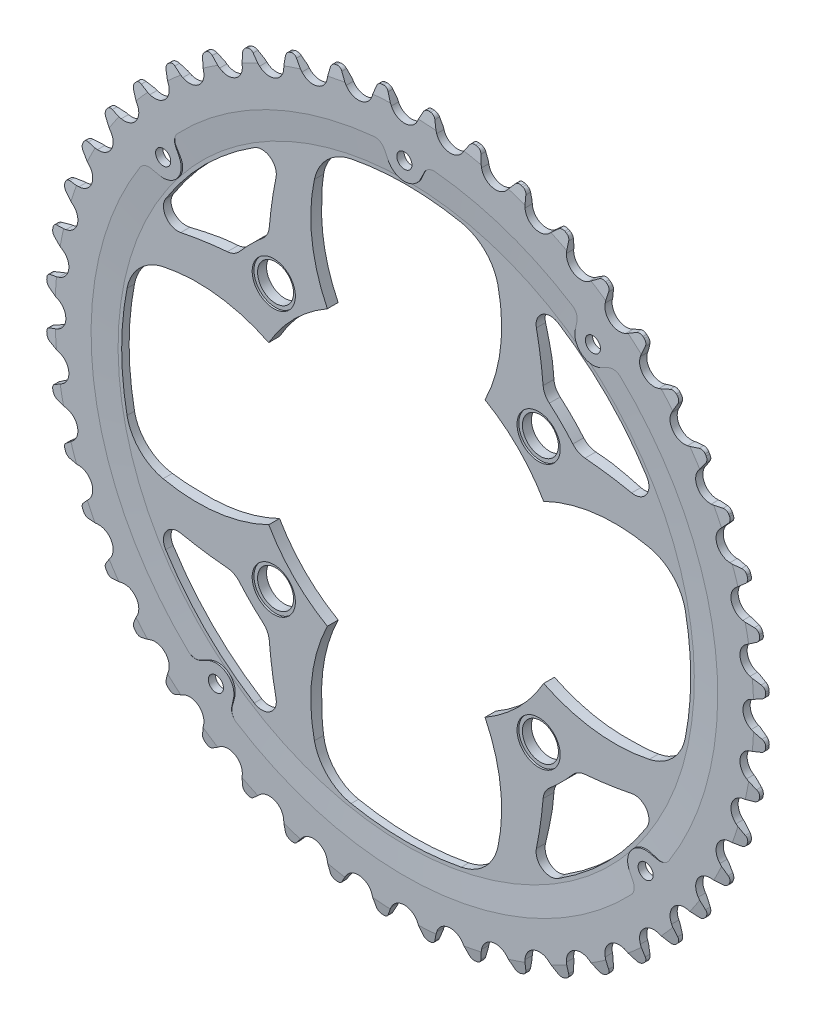
SolidWorks part; units mm, degrees
ref_plane "Plan de face" through (0, 0, 0) normal (0, 0, 1) x (1, 0, 0)
ref_plane "Plan de dessus" through (0, 0, 0) normal (0, 1, 0) x (1, 0, 0)
ref_plane "Plan de droite" through (0, 0, 0) normal (1, 0, 0) x (0, 0, -1)
sketch "Esquisse7" plane through (0, 0, 0) normal (1, 0, 0) x (0, 0, -1)
  line L0 (-21.1331, 0) -> (18.4676, 0) construction
  line L1 (0, 44) -> (2.5, 44)
  line L2 (-1, 100) -> (1, 100)
  line L3 (0, 0) -> (0, 124.4372) construction
  line L4 (2.5, 44) -> (2.5, 66)
  line L5 (-0.5, 80) -> (-1, 87)
  line L6 (-0.5, 44) -> (-0.5, 80)
  line L7 (1, 87) -> (2.5, 66)
  line L8 (-1, 87) -> (-1, 100)
  line L9 (1, 87) -> (1, 100)
  line L10 (2.5, 66) -> (2.5656, 65.8539) construction
  line L11 (-0.5, 80) -> (5.3022, 67.0831) construction
  line L12 (-0.5, 44) -> (0, 44)
  dimension "D1" = 88
  dimension "D2" = 200
  dimension "D4" = 2
  dimension "D5" = 2.5
  dimension "D6" = 160
  dimension "D7" = 174
  dimension "D3" = 3
revolve "Révolution1" add sketch "Esquisse7" angle 360 about L0
ref_plane "Plan1" through (0, 0, 0) normal (-0.788, 0.6157, 0) x (0, 0, 1)
sketch "Esquisse4" plane through (0, 0, 0) normal (1, 0, 0) x (0, 0, -1)
  line L0 (-6.7593, 0) -> (13.1966, 0) construction
  line L1 (-1, 100) -> (-0.5, 100)
  line L2 (-0.5, 100) -> (-1, 97)
  line L4 (-1, 97) -> (-1, 100)
  line L5 (0, 0) -> (0, 63.6893) construction
  line L6 (1, 100) -> (0.5, 100)
  line L7 (0.5, 100) -> (1, 97)
  line L8 (1, 97) -> (1, 100)
  line L9 (1, 100) -> (-1, 100) construction
  line L10 (-1, 100) -> (-1, -100) construction
  dimension "D1" = 3
  dimension "D2" = 1
revolve "Enlèvement de matière-Révolution1" cut sketch "Esquisse4" angle 360 about L0
sketch "Esquisse2" plane through (0, 0, 0) normal (0, 0, 1) x (1, 0, 0)
  line L0 (0, 0) -> (0, 69.4312) construction
  line L1 (-4.8509, 98.938) -> (-3.6252, 96.3095)
  line L2 (4.8509, 98.938) -> (3.6252, 96.3095)
  line L3 (0, 0) -> (87.6932, 0) construction
  arc A0 (-3.6252, 96.3095) -> (3.6252, 96.3095) centre (0, 98) ccw
  arc A1 (-4.8509, 98.938) -> (-6.3049, 99.801) centre (-6.2103, 98.304) ccw
  arc A2 (6.3049, 99.801) -> (-6.3049, 99.801) centre (0, 0) ccw
  arc A4 (4.8509, 98.938) -> (6.3049, 99.801) centre (6.2103, 98.304) cw
  circle A5 centre (0, 0) radius 100 construction
  dimension "D1" = 8
  dimension "D3" = 2
  dimension "D4" = 1.5
  dimension "D2" = 25
extrude "Enlèv. mat.-Extru.1" cut sketch "Esquisse2" against normal through all and the other way through all
pattern_circular "Répétition circulaire1" count 48 every 7.5 about axis through (0, 0, 0) along (0, 0, 1) of "Enlèv. mat.-Extru.1"
sketch "Esquisse5" plane through (0, 0, 0) normal (0, 0, 1) x (1, 0, 0)
  line L0 (0, 0) -> (40.1862, 0) construction
  line L1 (0, 0) -> (0, 40.1862) construction
  line L2 (0, 0) -> (-60.8251, 60.8251) construction
  line L3 (0, 0) -> (60.8251, 60.8251) construction
  circle A0 centre (0, 0) radius 52 construction
  circle A1 centre (-36.7696, 36.7696) radius 5
  circle A2 centre (36.7696, 36.7696) radius 5
  circle A3 centre (-36.7696, -36.7696) radius 5
  circle A4 centre (36.7696, -36.7696) radius 5
  dimension "D1" = 104
  dimension "D2" = 10
  dimension "D3" = 90
extrude "Enlèv. mat.-Extru.2" cut sketch "Esquisse5" against normal through all and the other way through all
sketch "Esquisse11" plane through (0, 0, 0.5) normal (0, 0, 1) x (1, 0, 0)
  circle A0 centre (36.7696, 36.7696) radius 6
  circle A1 centre (-36.7696, 36.7696) radius 6
  circle A2 centre (-36.7696, -36.7696) radius 6
  circle A3 centre (36.7696, -36.7696) radius 6
  circle A4 centre (36.7696, 36.7696) radius 5 construction
  circle A5 centre (-36.7696, 36.7696) radius 5 construction
  circle A6 centre (-36.7696, -36.7696) radius 5 construction
  circle A7 centre (36.7696, -36.7696) radius 5 construction
  dimension "D1" = 12
extrude "Enlèv. mat.-Extru.7" cut sketch "Esquisse11" against normal blind 0.5
sketch "Esquisse8" plane through (0, 0, 1) normal (0, 0, 1) x (1, 0, 0)
  line L0 (47.9272, 70.3104) -> (47.4405, 68.0205)
  line L1 (0, 0) -> (69.663, 89.1645) construction
  line L2 (56.6272, 63.5132) -> (54.5231, 62.4869)
  line L3 (0, 0) -> (110.6244, 0) construction
  line L4 (0, 0) -> (-3.7173, 30.2748) construction
  line L5 (0, 0) -> (-89.1645, 69.663) construction
  line L6 (-70.3104, 47.9272) -> (-68.0205, 47.4405)
  line L7 (-63.5132, 56.6272) -> (-62.4869, 54.5231)
  line L8 (-47.9272, -70.3104) -> (-47.4405, -68.0205)
  line L9 (-56.6272, -63.5132) -> (-54.5231, -62.4869)
  line L10 (70.3104, -47.9272) -> (68.0205, -47.4405)
  line L11 (63.5132, -56.6272) -> (62.4869, -54.5231)
  line L12 (0, 0) -> (8.1726, 23.7349) construction
  line L13 (-5.5202, 84.9123) -> (-4.494, 82.8081)
  line L14 (5.5202, 84.9123) -> (4.494, 82.8081)
  line L15 (0, 0) -> (0, 113.1514) construction
  arc A0 (47.4405, 68.0205) -> (54.5231, 62.4869) centre (52.3312, 66.9809) ccw
  circle A1 centre (0, 0) radius 87 construction
  circle A2 centre (0, 0) radius 85 construction
  arc A3 (60.0117, 62.9888) -> (56.6272, 63.5132) centre (57.9423, 60.8168) ccw
  arc A4 (46.5997, 73.4675) -> (47.9272, 70.3104) centre (44.9928, 70.9341) cw
  arc A5 (-73.4675, 46.5997) -> (-70.3104, 47.9272) centre (-70.9341, 44.9928) cw
  arc A6 (-62.4869, 54.5231) -> (-68.0205, 47.4405) centre (-66.9809, 52.3312) cw
  arc A7 (60.0117, 62.9888) -> (46.5997, 73.4675) centre (0, 0) ccw
  arc A8 (-62.9888, 60.0117) -> (-63.5132, 56.6272) centre (-60.8168, 57.9423) ccw
  arc A9 (-73.4675, 46.5997) -> (-62.9888, 60.0117) centre (0, 0) cw
  arc A10 (-46.5997, -73.4675) -> (-60.0117, -62.9888) centre (0, 0) cw
  arc A11 (-60.0117, -62.9888) -> (-56.6272, -63.5132) centre (-57.9423, -60.8168) ccw
  arc A12 (-46.5997, -73.4675) -> (-47.9272, -70.3104) centre (-44.9928, -70.9341) cw
  arc A13 (-54.5231, -62.4869) -> (-47.4405, -68.0205) centre (-52.3312, -66.9809) cw
  arc A14 (62.9888, -60.0117) -> (73.4675, -46.5997) centre (0, 0) ccw
  arc A15 (73.4675, -46.5997) -> (70.3104, -47.9272) centre (70.9341, -44.9928) cw
  arc A16 (68.0205, -47.4405) -> (62.4869, -54.5231) centre (66.9809, -52.3312) ccw
  arc A17 (62.9888, -60.0117) -> (63.5132, -56.6272) centre (60.8168, -57.9423) ccw
  arc A18 (-8.5101, 86.5828) -> (8.5101, 86.5828) centre (0, 0) cw
  arc A19 (8.5101, 86.5828) -> (5.5202, 84.9123) centre (8.2166, 83.5972) ccw
  arc A20 (-8.5101, 86.5828) -> (-5.5202, 84.9123) centre (-8.2166, 83.5972) cw
  arc A21 (4.494, 82.8081) -> (-4.494, 82.8081) centre (0, 85) cw
  dimension "D1" = 10
  dimension "D3" = 3
  dimension "D5" = 170
  dimension "D2" = 38
  dimension "D4" = 52
  dimension "D6" = 90
extrude "Extrusion1" add sketch "Esquisse8" against normal up to surface up to face at (80, 0, 0.5)
sketch "Esquisse9" plane through (0, 0, -1) normal (0, 0, -1) x (-1, 0, 0)
  line L0 (-47.4405, 68.0205) -> (-47.9272, 70.3104) construction
  line L1 (-56.6272, 63.5132) -> (-54.5231, 62.4869) construction
  line L2 (-47.4405, 68.0205) -> (-47.9272, 70.3104)
  line L3 (-56.6272, 63.5132) -> (-54.5231, 62.4869)
  line L4 (70.3104, 47.9272) -> (68.0205, 47.4405) construction
  line L5 (62.4869, 54.5231) -> (63.5132, 56.6272) construction
  line L6 (70.3104, 47.9272) -> (68.0205, 47.4405)
  line L7 (62.4869, 54.5231) -> (63.5132, 56.6272)
  line L8 (54.5231, -62.4869) -> (56.6272, -63.5132) construction
  line L9 (47.9272, -70.3104) -> (47.4405, -68.0205) construction
  line L10 (54.5231, -62.4869) -> (56.6272, -63.5132)
  line L11 (47.9272, -70.3104) -> (47.4405, -68.0205)
  line L12 (-70.3104, -47.9272) -> (-68.0205, -47.4405) construction
  line L13 (-62.4869, -54.5231) -> (-63.5132, -56.6272) construction
  line L14 (-70.3104, -47.9272) -> (-68.0205, -47.4405)
  line L15 (-62.4869, -54.5231) -> (-63.5132, -56.6272)
  line L16 (-4.494, 82.8081) -> (-5.5202, 84.9123) construction
  line L17 (5.5202, 84.9123) -> (4.494, 82.8081) construction
  line L18 (-4.494, 82.8081) -> (-5.5202, 84.9123)
  line L19 (5.5202, 84.9123) -> (4.494, 82.8081)
  arc A0 (-46.5997, 73.4675) -> (-47.9272, 70.3104) centre (-44.9928, 70.9341) ccw construction
  arc A1 (-49.2529, 63.0409) -> (-47.4405, 68.0205) centre (-52.3312, 66.9809) ccw construction
  arc A2 (-54.5231, 62.4869) -> (-49.2529, 63.0409) centre (-52.3312, 66.9809) ccw construction
  arc A3 (-56.6272, 63.5132) -> (-60.0117, 62.9888) centre (-57.9423, 60.8168) ccw construction
  arc A4 (-46.5997, 73.4675) -> (-47.9272, 70.3104) centre (-44.9928, 70.9341) ccw
  arc A5 (-49.2529, 63.0409) -> (-47.4405, 68.0205) centre (-52.3312, 66.9809) ccw
  arc A6 (-54.5231, 62.4869) -> (-49.2529, 63.0409) centre (-52.3312, 66.9809) ccw
  arc A7 (-56.6272, 63.5132) -> (-60.0117, 62.9888) centre (-57.9423, 60.8168) ccw
  arc A8 (-46.5997, 73.4675) -> (-60.0117, 62.9888) centre (0, 0) ccw
  arc A9 (-8.5101, 86.5828) -> (-46.5997, 73.4675) centre (0, 0) ccw construction
  arc A10 (73.4675, 46.5997) -> (70.3104, 47.9272) centre (70.9341, 44.9928) ccw construction
  arc A11 (62.4869, 54.5231) -> (68.0205, 47.4405) centre (66.9809, 52.3312) ccw construction
  arc A12 (63.5132, 56.6272) -> (62.9888, 60.0117) centre (60.8168, 57.9423) ccw construction
  arc A13 (73.4675, 46.5997) -> (70.3104, 47.9272) centre (70.9341, 44.9928) ccw
  arc A14 (62.4869, 54.5231) -> (68.0205, 47.4405) centre (66.9809, 52.3312) ccw
  arc A15 (63.5132, 56.6272) -> (62.9888, 60.0117) centre (60.8168, 57.9423) ccw
  arc A16 (62.9888, 60.0117) -> (73.4675, 46.5997) centre (0, 0) cw
  arc A17 (-8.5101, 86.5828) -> (-46.5997, 73.4675) centre (0, 0) ccw construction
  arc A18 (54.5231, -62.4869) -> (47.4405, -68.0205) centre (52.3312, -66.9809) ccw construction
  arc A19 (56.6272, -63.5132) -> (60.0117, -62.9888) centre (57.9423, -60.8168) ccw construction
  arc A20 (46.5997, -73.4675) -> (47.9272, -70.3104) centre (44.9928, -70.9341) ccw construction
  arc A21 (54.5231, -62.4869) -> (47.4405, -68.0205) centre (52.3312, -66.9809) ccw
  arc A22 (56.6272, -63.5132) -> (60.0117, -62.9888) centre (57.9423, -60.8168) ccw
  arc A23 (46.5997, -73.4675) -> (47.9272, -70.3104) centre (44.9928, -70.9341) ccw
  arc A24 (60.0117, -62.9888) -> (46.5997, -73.4675) centre (0, 0) cw
  arc A25 (-62.9888, -60.0117) -> (46.5997, -73.4675) centre (0, 0) ccw construction
  arc A26 (-73.4675, -46.5997) -> (-70.3104, -47.9272) centre (-70.9341, -44.9928) ccw construction
  arc A27 (-62.4869, -54.5231) -> (-68.0205, -47.4405) centre (-66.9809, -52.3312) ccw construction
  arc A28 (-63.5132, -56.6272) -> (-62.9888, -60.0117) centre (-60.8168, -57.9423) ccw construction
  arc A29 (-73.4675, -46.5997) -> (-70.3104, -47.9272) centre (-70.9341, -44.9928) ccw
  arc A30 (-62.4869, -54.5231) -> (-68.0205, -47.4405) centre (-66.9809, -52.3312) ccw
  arc A31 (-63.5132, -56.6272) -> (-62.9888, -60.0117) centre (-60.8168, -57.9423) ccw
  arc A32 (-62.9888, -60.0117) -> (-73.4675, -46.5997) centre (0, 0) cw
  arc A33 (-60.0117, 62.9888) -> (-73.4675, -46.5997) centre (0, 0) ccw construction
  arc A34 (-5.5202, 84.9123) -> (-8.5101, 86.5828) centre (-8.2166, 83.5972) ccw construction
  arc A35 (-4.494, 82.8081) -> (4.494, 82.8081) centre (0, 85) ccw construction
  arc A36 (8.5101, 86.5828) -> (5.5202, 84.9123) centre (8.2166, 83.5972) ccw construction
  arc A37 (-5.5202, 84.9123) -> (-8.5101, 86.5828) centre (-8.2166, 83.5972) ccw
  arc A38 (-4.494, 82.8081) -> (4.494, 82.8081) centre (0, 85) ccw
  arc A39 (8.5101, 86.5828) -> (5.5202, 84.9123) centre (8.2166, 83.5972) ccw
  arc A40 (-8.5101, 86.5828) -> (8.5101, 86.5828) centre (0, 0) cw
  arc A41 (-8.5101, 86.5828) -> (-46.5997, 73.4675) centre (0, 0) ccw construction
extrude "Enlèv. mat.-Extru.5" cut sketch "Esquisse9" along normal through all
sketch "Esquisse6" plane through (0, 0, 0) normal (0, 0, 1) x (1, 0, 0)
  circle A1 centre (52.3312, 66.9809) radius 2.1
  circle A2 centre (-66.9809, 52.3312) radius 2.1
  circle A3 centre (-52.3312, -66.9809) radius 2.1
  circle A4 centre (66.9809, -52.3312) radius 2.1
  arc A5 (47.4405, 68.0205) -> (54.5231, 62.4869) centre (52.3312, 66.9809) ccw construction
  arc A6 (68.0205, -47.4405) -> (62.4869, -54.5231) centre (66.9809, -52.3312) ccw construction
  arc A7 (-47.4405, -68.0205) -> (-54.5231, -62.4869) centre (-52.3312, -66.9809) ccw construction
  arc A8 (-68.0205, 47.4405) -> (-62.4869, 54.5231) centre (-66.9809, 52.3312) ccw construction
  circle A9 centre (0, 85) radius 2.1
  arc A11 (-4.494, 82.8081) -> (4.494, 82.8081) centre (0, 85) ccw construction
  dimension "D2" = 4.2
extrude "Enlèv. mat.-Extru.4" cut sketch "Esquisse6" against normal through all and the other way through all
sketch "Esquisse10" plane through (0, 0, 0.5) normal (0, 0, 1) x (1, 0, 0)
  line L0 (0, 0) -> (115.5873, 0) construction
  line L1 (0, 0) -> (0, 64.2408) construction
  line L2 (0, 0) -> (50.0683, 50.0683) construction
  arc A0 (77.5048, -15.297) -> (77.5048, 15.297) centre (0, 0) ccw
  arc A1 (38.1664, 21.8934) -> (67.4934, 25.4872) centre (58, -18.5) cw
  arc A3 (38.1664, -21.8934) -> (67.4934, -25.4872) centre (58, 18.5) ccw
  arc A4 (38.1664, -21.8934) -> (38.1664, 21.8934) centre (0, 0) ccw
  circle A5 centre (0, 0) radius 44 construction
  arc A6 (77.5048, 15.297) -> (67.4934, 25.4872) centre (64.7509, 12.7798) ccw
  arc A7 (67.4934, -25.4872) -> (77.5048, -15.297) centre (64.7509, -12.7798) ccw
  arc A8 (-67.4934, -25.4872) -> (-77.5048, -15.297) centre (-64.7509, -12.7798) cw
  arc A9 (-77.5048, 15.297) -> (-67.4934, 25.4872) centre (-64.7509, 12.7798) cw
  arc A10 (-38.1664, -21.8934) -> (-38.1664, 21.8934) centre (0, 0) cw
  arc A11 (-38.1664, -21.8934) -> (-67.4934, -25.4872) centre (-58, 18.5) cw
  arc A12 (-38.1664, 21.8934) -> (-67.4934, 25.4872) centre (-58, -18.5) ccw
  arc A13 (-77.5048, -15.297) -> (-77.5048, 15.297) centre (0, 0) cw
  arc A14 (-15.297, -77.5048) -> (15.297, -77.5048) centre (0, 0) ccw
  arc A15 (21.8934, -38.1664) -> (25.4872, -67.4934) centre (-18.5, -58) cw
  arc A16 (-21.8934, -38.1664) -> (-25.4872, -67.4934) centre (18.5, -58) ccw
  arc A17 (-21.8934, -38.1664) -> (21.8934, -38.1664) centre (0, 0) ccw
  arc A18 (15.297, -77.5048) -> (25.4872, -67.4934) centre (12.7798, -64.7509) ccw
  arc A19 (-25.4872, -67.4934) -> (-15.297, -77.5048) centre (-12.7798, -64.7509) ccw
  arc A20 (-25.4872, 67.4934) -> (-15.297, 77.5048) centre (-12.7798, 64.7509) cw
  arc A21 (15.297, 77.5048) -> (25.4872, 67.4934) centre (12.7798, 64.7509) cw
  arc A22 (-21.8934, 38.1664) -> (21.8934, 38.1664) centre (0, 0) cw
  arc A23 (-21.8934, 38.1664) -> (-25.4872, 67.4934) centre (18.5, 58) cw
  arc A24 (21.8934, 38.1664) -> (25.4872, 67.4934) centre (-18.5, 58) ccw
  arc A25 (-15.297, 77.5048) -> (15.297, 77.5048) centre (0, 0) cw
  dimension "D1" = 158
  dimension "D2" = 45
  dimension "D5" = 13
  dimension "D3" = 53
  dimension "D4" = 58
extrude "Enlèv. mat.-Extru.6" cut sketch "Esquisse10" against normal blind 10
sketch "Esquisse12" plane through (0, 0, 0.5) normal (0, 0, 1) x (1, 0, 0)
  line L0 (0, 0) -> (77.9394, 77.9394) construction
  line L1 (0, 0) -> (0, 47.1067) construction
  line L2 (0, 0) -> (-77.9394, 77.9394) construction
  line L3 (0, 0) -> (36.1484, 0) construction
  arc A0 (66.7823, 42.2033) -> (42.2033, 66.7823) centre (0, 0) ccw
  arc A1 (46.2772, 39.7419) -> (39.7419, 46.2772) centre (0, 0) ccw
  arc A2 (49.6515, 38.017) -> (62.5951, 36.1484) centre (40.4344, -71.5962) cw
  arc A3 (38.017, 49.6515) -> (36.1484, 62.5951) centre (-71.5962, 40.4344) ccw
  arc A4 (42.2033, 66.7823) -> (36.1484, 62.5951) centre (40.0664, 63.401) ccw
  arc A5 (66.7823, 42.2033) -> (62.5951, 36.1484) centre (63.401, 40.0664) cw
  arc A6 (38.017, 49.6515) -> (39.7419, 46.2772) centre (42.9994, 50.0705) ccw
  arc A7 (49.6515, 38.017) -> (46.2772, 39.7419) centre (50.0705, 42.9994) cw
  arc A8 (-49.6515, 38.017) -> (-46.2772, 39.7419) centre (-50.0705, 42.9994) ccw
  arc A9 (-38.017, 49.6515) -> (-39.7419, 46.2772) centre (-42.9994, 50.0705) cw
  arc A10 (-66.7823, 42.2033) -> (-62.5951, 36.1484) centre (-63.401, 40.0664) ccw
  arc A11 (-42.2033, 66.7823) -> (-36.1484, 62.5951) centre (-40.0664, 63.401) cw
  arc A12 (-38.017, 49.6515) -> (-36.1484, 62.5951) centre (71.5962, 40.4344) cw
  arc A13 (-49.6515, 38.017) -> (-62.5951, 36.1484) centre (-40.4344, -71.5962) ccw
  arc A14 (-46.2772, 39.7419) -> (-39.7419, 46.2772) centre (0, 0) cw
  arc A15 (-66.7823, 42.2033) -> (-42.2033, 66.7823) centre (0, 0) cw
  arc A16 (-66.7823, -42.2033) -> (-42.2033, -66.7823) centre (0, 0) ccw
  arc A17 (-46.2772, -39.7419) -> (-39.7419, -46.2772) centre (0, 0) ccw
  arc A18 (-49.6515, -38.017) -> (-62.5951, -36.1484) centre (-40.4344, 71.5962) cw
  arc A19 (-38.017, -49.6515) -> (-36.1484, -62.5951) centre (71.5962, -40.4344) ccw
  arc A20 (-42.2033, -66.7823) -> (-36.1484, -62.5951) centre (-40.0664, -63.401) ccw
  arc A21 (-66.7823, -42.2033) -> (-62.5951, -36.1484) centre (-63.401, -40.0664) cw
  arc A22 (-38.017, -49.6515) -> (-39.7419, -46.2772) centre (-42.9994, -50.0705) ccw
  arc A23 (-49.6515, -38.017) -> (-46.2772, -39.7419) centre (-50.0705, -42.9994) cw
  arc A24 (49.6515, -38.017) -> (46.2772, -39.7419) centre (50.0705, -42.9994) ccw
  arc A25 (38.017, -49.6515) -> (39.7419, -46.2772) centre (42.9994, -50.0705) cw
  arc A26 (66.7823, -42.2033) -> (62.5951, -36.1484) centre (63.401, -40.0664) ccw
  arc A27 (42.2033, -66.7823) -> (36.1484, -62.5951) centre (40.0664, -63.401) cw
  arc A28 (38.017, -49.6515) -> (36.1484, -62.5951) centre (-71.5962, -40.4344) cw
  arc A29 (49.6515, -38.017) -> (62.5951, -36.1484) centre (40.4344, 71.5962) ccw
  arc A30 (46.2772, -39.7419) -> (39.7419, -46.2772) centre (0, 0) cw
  arc A31 (66.7823, -42.2033) -> (42.2033, -66.7823) centre (0, 0) cw
  point P12 (33.9791, 71.3192)
  point P15 (71.3192, 33.9791)
  point P18 (38.1714, 47.5809)
  point P21 (47.5809, 38.1714)
  point P40 (-47.5809, 38.1714)
  point P41 (-38.1714, 47.5809)
  point P42 (-71.3192, 33.9791)
  point P43 (-33.9791, 71.3192)
  point P72 (-33.9791, -71.3192)
  point P73 (-71.3192, -33.9791)
  point P74 (-38.1714, -47.5809)
  point P75 (-47.5809, -38.1714)
  point P76 (47.5809, -38.1714)
  point P77 (38.1714, -47.5809)
  point P78 (71.3192, -33.9791)
  point P79 (33.9791, -71.3192)
  dimension "D1" = 122
  dimension "D2" = 158
  dimension "D3" = 110
  dimension "D4" = 4
  dimension "D5" = 33
  dimension "D6" = 5
  dimension "D7" = 10
extrude "Enlèv. mat.-Extru.8" cut sketch "Esquisse12" against normal through all
